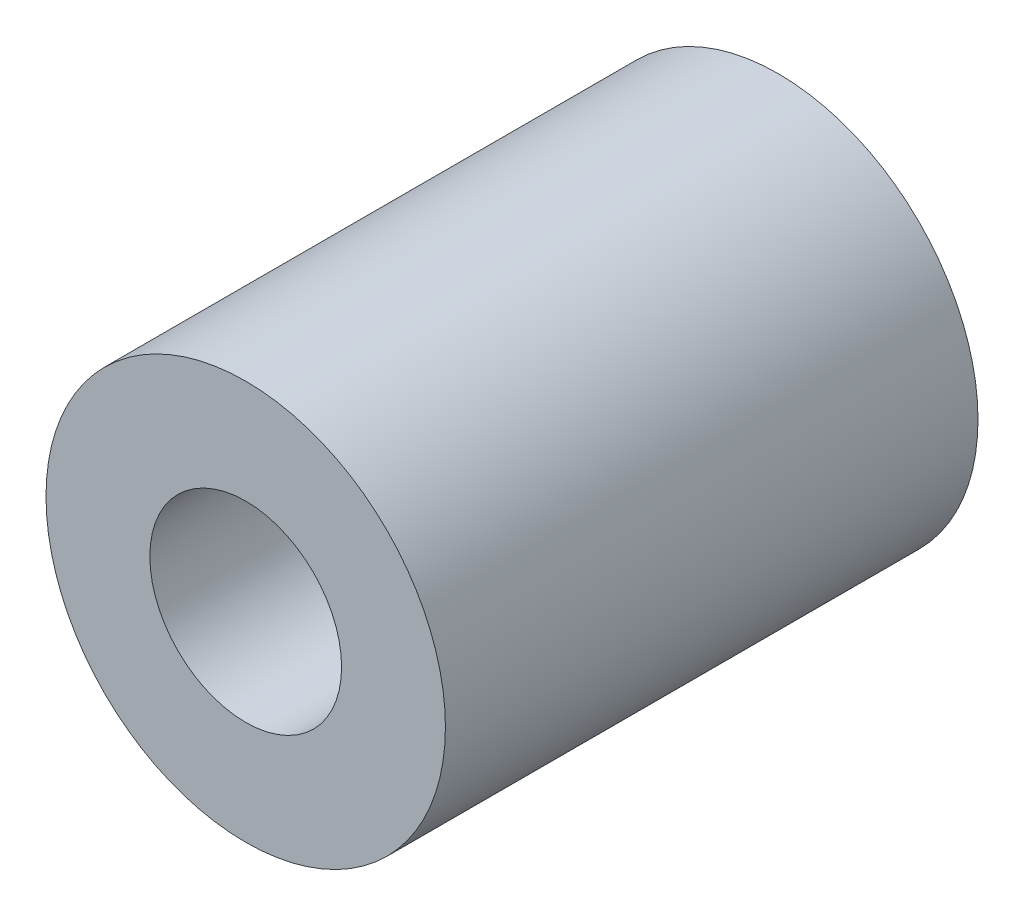
SolidWorks part; units mm, degrees
ref_plane "Front Plane" through (0, 0, 0) normal (0, 0, 1) x (1, 0, 0)
ref_plane "Top Plane" through (0, 0, 0) normal (0, 1, 0) x (1, 0, 0)
ref_plane "Right Plane" through (0, 0, 0) normal (1, 0, 0) x (0, 0, -1)
sketch "Sketch1" plane through (0, 0, 0) normal (0, 0, 1) x (1, 0, 0)
  circle A0 centre (0, 0) radius 2.3813
  circle A1 centre (0, 0) radius 1.143
  dimension "OD" = 4.7625
  dimension "ID" = 2.286
extrude "Extrude1" add sketch "Sketch1" along normal mid plane 6.35
sketch "Sketch2" plane through (0, 0, 0) normal (1, 0, 0) x (0, 0, -1)
  line L0 (-3.175, -1.143) -> (3.175, -1.143) construction
  line L3 (3.175, 1.143) -> (-3.175, 1.143) construction
  line L5 (-3.175, -1.143) -> (3.175, -1.143)
  line L6 (3.175, 1.143) -> (-3.175, 1.143)
sketch "Sketch4" plane through (0, 0, 3.175) normal (0, 0, 1) x (1, 0, 0)
  line L0 (0, 0) -> (-0.8082, 0.8082)
  line L1 (0, -1.7463) -> (0, 1.7463) construction
  circle A0 centre (0, 0) radius 1.143 construction
  dimension "D1" = 45
